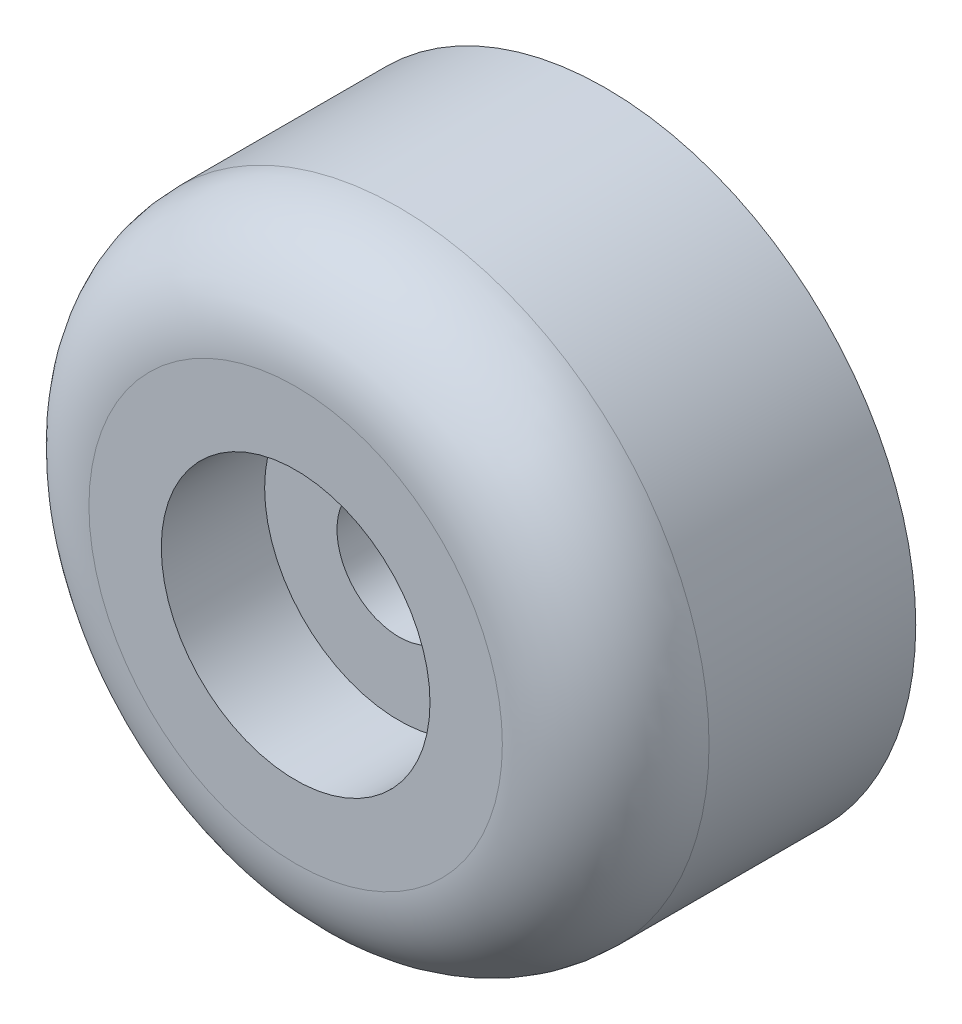
SolidWorks part; units mm, degrees
ref_plane "Ön Düzlem" through (0, 0, 0) normal (0, 0, 1) x (1, 0, 0)
ref_plane "Üst Düzlem" through (0, 0, 0) normal (0, 1, 0) x (1, 0, 0)
ref_plane "Sağ Düzlem" through (0, 0, 0) normal (1, 0, 0) x (0, 0, -1)
sketch "Çizim1" plane through (0, 0, 0) normal (0, 0, 1) x (1, 0, 0)
  circle A0 centre (0, 0) radius 15
  dimension "D1" = 30
extrude "Yükseklik-Ekstrüzyon1" add sketch "Çizim1" along normal blind 15
fillet "Radyus1" radius 5 1 edges at (15, 0, 15)
sketch "Çizim2" plane through (0, 0, 0) normal (0, 0, -1) x (-1, 0, 0)
  circle A0 centre (0, 0) radius 3
  dimension "D1" = 6
extrude "Kes-Ekstrüzyon1" cut sketch "Çizim2" against normal blind 15
sketch "Çizim3" plane through (0, 0, 15) normal (0, 0, 1) x (1, 0, 0)
  circle A0 centre (0, 0) radius 6.5
  dimension "D1" = 13
extrude "Kes-Ekstrüzyon2" cut sketch "Çizim3" against normal blind 5
fillet "Radyus2" radius 0.5 1 edges at (-3, 0, 0)
